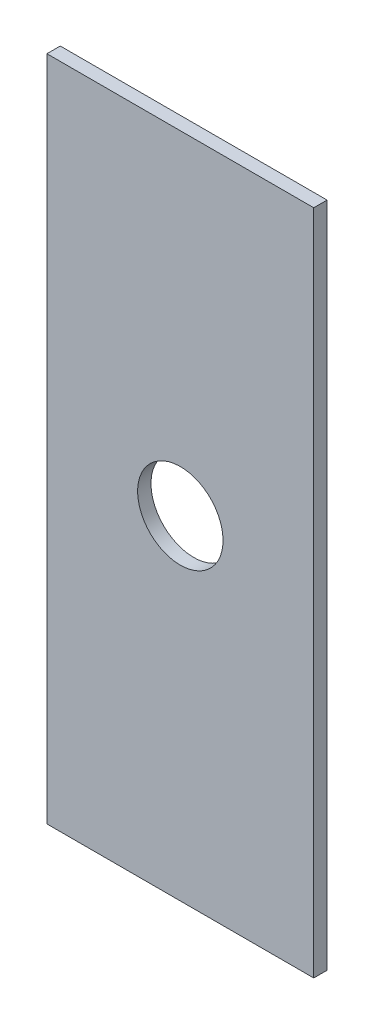
SolidWorks part; units mm, degrees
ref_plane "Front Plane" through (0, 0, 0) normal (0, 0, 1) x (1, 0, 0)
ref_plane "Top Plane" through (0, 0, 0) normal (0, 1, 0) x (1, 0, 0)
ref_plane "Right Plane" through (0, 0, 0) normal (1, 0, 0) x (0, 0, -1)
sketch "Sketch1" plane through (0, 0, 0) normal (0, 0, 1) x (1, 0, 0)
  line L1 (-59.1652, 12.6391) -> (0.8348, 12.6391)
  line L2 (-59.1652, 12.6391) -> (-59.1652, -137.3609)
  line L3 (-59.1652, -137.3609) -> (0.8348, -137.3609)
  line L4 (0.8348, 12.6391) -> (0.8348, -137.3609)
  line L5 (-59.1652, 12.6391) -> (0.8348, -137.3609) construction
  line L6 (-59.1652, -137.3609) -> (0.8348, 12.6391) construction
  circle A0 centre (-29.1652, -62.3609) radius 9.6
  point P0 (-29.1652, -62.3609)
  dimension "D3" = 19.2
  dimension "D4" = 75
  dimension "D5" = 30
  dimension "D1" = 60
  dimension "D2" = 150
extrude "Boss-Extrude1" add sketch "Sketch1" along normal blind 3
